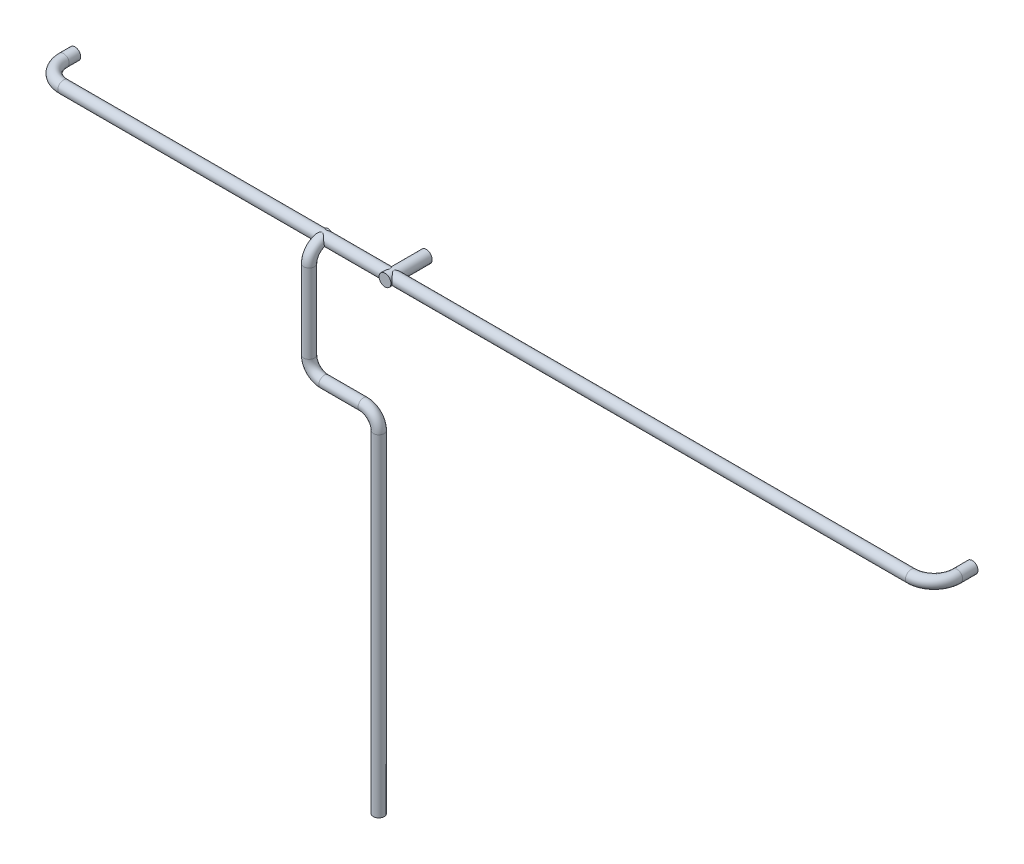
SolidWorks part; units mm, degrees
ref_plane "Alzado" through (0, 0, 0) normal (0, 0, 1) x (1, 0, 0)
ref_plane "Planta" through (0, 0, 0) normal (0, 1, 0) x (1, 0, 0)
ref_plane "Vista lateral" through (0, 0, 0) normal (1, 0, 0) x (0, 0, -1)
sketch "Croquis1" plane through (0, 0, 0) normal (0, 0, 1) x (1, 0, 0)
  circle A0 centre (0, 0) radius 9.5
  dimension "D1" = 19
sketch3d "Croquis3D1"
  line L0 (0, 0, 0) -> (0, 0, 15)
  line L1 (30, 0, 45) -> (1140, 0, 45)
  line L2 (1170, 0, 15) -> (1170, 0, -5)
  arc A0 (1140, 0, 45) -> (1170, 0, 15) centre (1140, 0, 15) ccw
  arc A1 (0, 0, 15) -> (30, 0, 45) centre (30, 0, 15) ccw
  point P7 (1170, 0, 45)
  point P8 (1140, 30, 15)
  point P11 (0, 0, 45)
  point P12 (30, 30, 15)
  dimension "D4" = 30
  dimension "D1" = 1170
  dimension "D2" = 50
  dimension "D3" = 45
sweep "Barrer1" add path "Croquis3D1" circular profile diameter 15 parameters "D3"=15
sketch "Croquis22" plane through (0, 0, 0) normal (0, 0, -1) x (-1, 0, 0)
  line L0 (0, 0) -> (-460, 0)
  circle A0 centre (-460, 0) radius 7.8066
  dimension "D1" = 460
extrude "Saliente-Extruir1" add sketch "Croquis22" against normal blind 54
ref_plane "Plano1" through (0, 0, 40) normal (0, 0, 1) x (1, 0, 0)
sketch "Croquis27" plane through (0, 0, 40) normal (0, 0, 1) x (1, 0, 0)
  circle A0 centre (371.6247, 0) radius 7.1003
sketch3d "Croquis3D2"
  line L0 (371.6247, 0, 40) -> (371.6247, 0, 45.0651)
  line L1 (371.6247, -20, 65.0651) -> (371.6247, -123.5494, 65.0651)
  line L2 (391.6247, -143.5494, 65.0651) -> (442.9154, -143.5494, 65.0651)
  line L3 (462.9154, -163.5494, 65.0651) -> (462.9154, -597.97, 65.0651)
  arc A0 (371.6247, 0, 45.0651) -> (371.6247, -20, 65.0651) centre (371.6247, -20, 45.0651) ccw
  arc A1 (442.9154, -143.5494, 65.0651) -> (462.9154, -163.5494, 65.0651) centre (442.9154, -163.5494, 65.0651) ccw
  arc A2 (371.6247, -123.5494, 65.0651) -> (391.6247, -143.5494, 65.0651) centre (391.6247, -123.5494, 65.0651) ccw
  point P6 (371.6247, 0, 65.0651)
  point P7 (391.6247, -20, 45.0651)
  point P12 (462.9154, -143.5494, 65.0651)
  point P13 (442.9154, -163.5494, 45.0651)
  point P16 (371.6247, -143.5494, 65.0651)
  point P17 (391.6247, -123.5494, 85.0651)
  point P18 (462.9154, -597.97, 65.0651)
  dimension "D1" = 20
  dimension "D2" = 20
sweep "Barrer3" add profiles "Croquis27" path "Croquis3D2"
